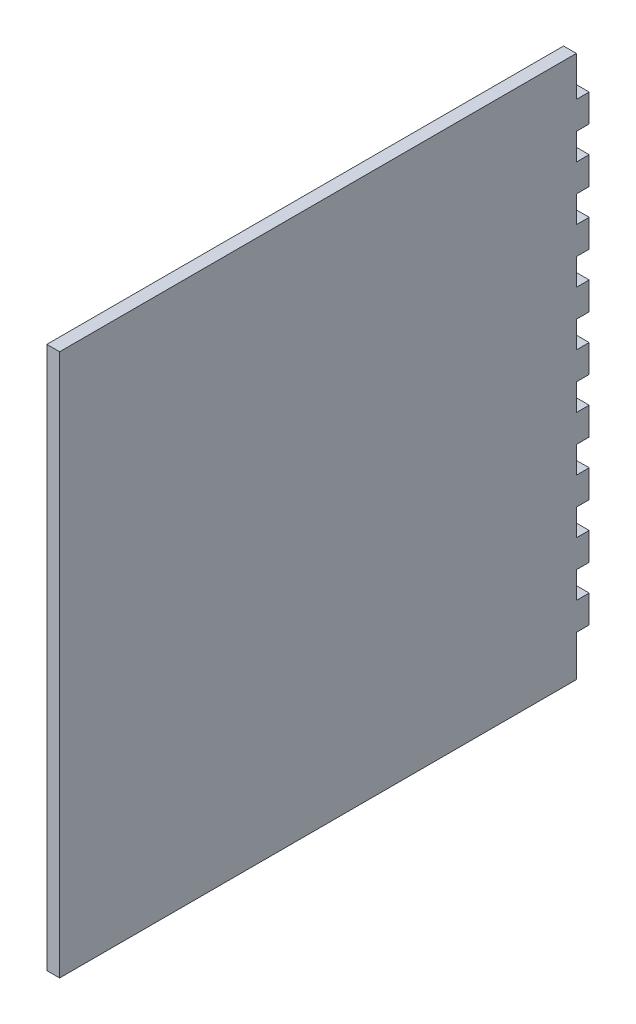
SolidWorks part; units mm, degrees
ref_plane "Front Plane" through (0, 0, 0) normal (0, 0, 1) x (1, 0, 0)
ref_plane "Top Plane" through (0, 0, 0) normal (0, 1, 0) x (1, 0, 0)
ref_plane "Right Plane" through (0, 0, 0) normal (1, 0, 0) x (0, 0, -1)
sketch "Sketch1" plane through (0, 0, 0) normal (1, 0, 0) x (0, 0, -1)
  line L0 (121.0056, 0) -> (121.0056, -9.3345)
  line L1 (0, 0) -> (121.0056, 0)
  line L2 (0, 0) -> (0, -127)
  line L3 (0, -127) -> (121.0056, -127)
  line L4 (121.0056, 0) -> (121.0056, -127) construction
  line L5 (121.0056, -9.3345) -> (124.0028, -9.3345)
  line L6 (124.0028, -9.3345) -> (124.0028, -15.8115)
  line L7 (124.0028, -15.8115) -> (121.0056, -15.8115)
  line L8 (121.0056, -15.8115) -> (121.0056, -22.0345)
  line L9 (121.0056, -22.0345) -> (124.0028, -22.0345)
  line L10 (124.0028, -22.0345) -> (124.0028, -28.5115)
  line L11 (124.0028, -28.5115) -> (121.0056, -28.5115)
  line L12 (121.0056, -28.5115) -> (121.0056, -34.7345)
  line L13 (121.0056, -34.7345) -> (124.0028, -34.7345)
  line L14 (124.0028, -34.7345) -> (124.0028, -41.2115)
  line L15 (124.0028, -41.2115) -> (121.0056, -41.2115)
  line L16 (121.0056, -41.2115) -> (121.0056, -47.4345)
  line L17 (121.0056, -47.4345) -> (124.0028, -47.4345)
  line L18 (124.0028, -47.4345) -> (124.0028, -53.9115)
  line L19 (124.0028, -53.9115) -> (121.0056, -53.9115)
  line L20 (121.0056, -53.9115) -> (121.0056, -60.1345)
  line L21 (121.0056, -60.1345) -> (124.0028, -60.1345)
  line L22 (124.0028, -60.1345) -> (124.0028, -66.6115)
  line L23 (124.0028, -66.6115) -> (121.0056, -66.6115)
  line L24 (121.0056, -66.6115) -> (121.0056, -72.8345)
  line L25 (121.0056, -72.8345) -> (124.0028, -72.8345)
  line L26 (124.0028, -72.8345) -> (124.0028, -79.3115)
  line L27 (124.0028, -79.3115) -> (121.0056, -79.3115)
  line L28 (121.0056, -79.3115) -> (121.0056, -85.5345)
  line L29 (121.0056, -85.5345) -> (124.0028, -85.5345)
  line L30 (124.0028, -85.5345) -> (124.0028, -92.0115)
  line L31 (124.0028, -92.0115) -> (121.0056, -92.0115)
  line L32 (121.0056, -92.0115) -> (121.0056, -98.2345)
  line L33 (121.0056, -98.2345) -> (124.0028, -98.2345)
  line L34 (124.0028, -98.2345) -> (124.0028, -104.7115)
  line L35 (124.0028, -104.7115) -> (121.0056, -104.7115)
  line L36 (121.0056, -104.7115) -> (121.0056, -110.9345)
  line L37 (121.0056, -110.9345) -> (124.0028, -110.9345)
  line L38 (124.0028, -110.9345) -> (124.0028, -117.4115)
  line L39 (124.0028, -117.4115) -> (121.0056, -117.4115)
  line L40 (121.0056, -117.4115) -> (121.0056, -127)
  line L41 (121.0056, -117.4115) -> (121.0056, -123.6345) [skipped]
  dimension "D1" = 121.0056
  dimension "D2" = 127
  dimension "D3" = 2.9972
  dimension "D4" = 6.477
  dimension "D5" = 6.223
  dimension "D6" = 9.3345
  dimension "D7" = 9
extrude "Boss-Extrude1" add sketch "Sketch1" along normal blind 2.9972
